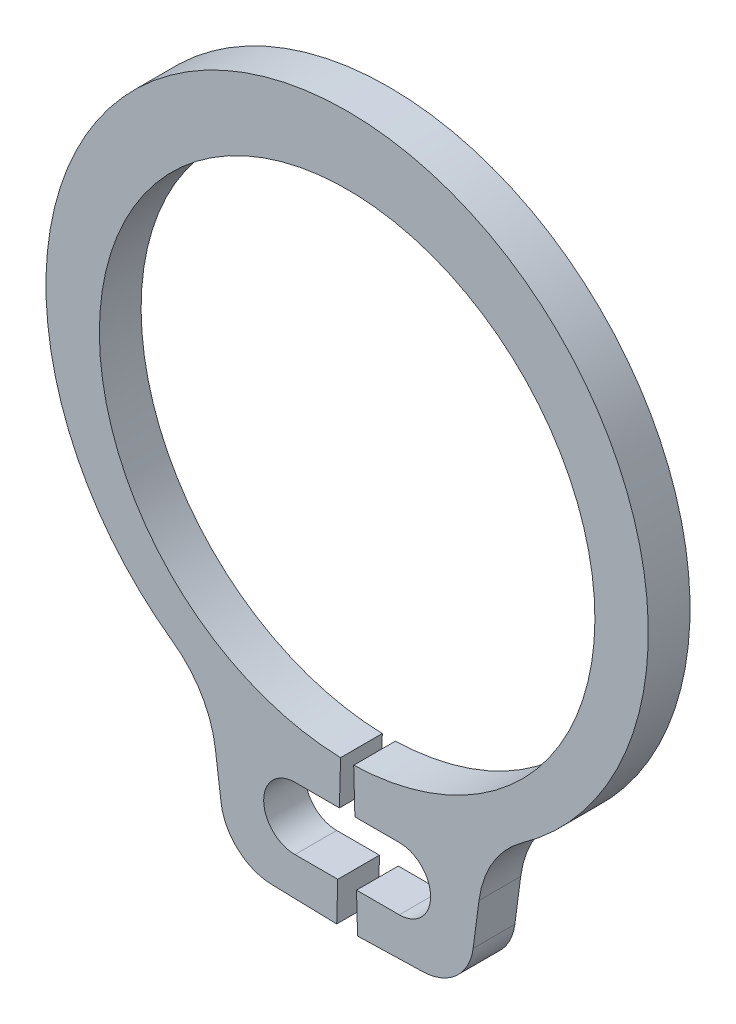
SolidWorks part; units mm, degrees
ref_plane "Plane1" through (0, 0, 0) normal (0, 0, 1) x (1, 0, 0)
ref_plane "Plane2" through (0, 0, 0) normal (0, 1, 0) x (1, 0, 0)
ref_plane "Plane3" through (0, 0, 0) normal (1, 0, 0) x (0, 0, -1)
sketch "Clipboard" plane through (0, 0, 0) normal (0, 0, 1) x (1, 0, 0)
  line L0 (0, 0) -> (0.65, 0)
  line L1 (0, 0) -> (0, 0.4)
  line L2 (0, 0) -> (0, -1.4)
  circle A0 centre (0, 0) radius 0.3
  circle A1 centre (0, 0) radius 2.5
  dimension "HoleDia" = 0.6
  dimension "ShaftDia" = 5
  dimension "LargeSection" = 0.65
  dimension "SmallSection" = 0.4
  dimension "LugSection" = 1.4
sketch "BodySke" plane through (0, 0, 0) normal (0, 0, 1) x (1, 0, 0)
  line L0 (-1.5431, 0) -> (1.5431, 0) construction
  line L1 (0, 0) -> (0, 3.025) construction
  line L2 (0.0629, -2.3742) -> (0.1, -3.7737)
  line L3 (-0.0629, -2.3742) -> (-0.1, -3.7737)
  line L4 (0, 0) -> (2.255, -3.0275) construction
  line L5 (0, 0) -> (-2.255, -3.0275) construction
  line L6 (0.1, -3.7737) -> (0.7253, -3.7571)
  line L7 (1.2638, -2.897) -> (1.2078, -3.3225)
  line L8 (-1.2638, -2.897) -> (-1.2078, -3.3225)
  line L9 (-0.1, -3.7737) -> (-0.7253, -3.7571)
  circle A0 centre (0, 0) radius 2.375 construction
  arc A1 (0.0629, -2.3742) -> (-0.0629, -2.3742) centre (0, 0) ccw
  arc A2 (1.6576, -2.2255) -> (-1.6576, -2.2255) centre (0, 0.1381) ccw construction
  arc A3 (0.1, -3.7737) -> (0.9453, -3.6547) centre (0, 0) ccw construction
  arc A4 (1.6749, -2.2133) -> (1.2638, -2.897) centre (2.255, -3.0275) ccw
  arc A5 (-1.2638, -2.897) -> (-1.6749, -2.2133) centre (-2.255, -3.0275) ccw
  arc A6 (-0.9453, -3.6547) -> (-0.1, -3.7737) centre (0, 0) ccw construction
  arc A7 (1.6749, -2.2133) -> (-1.6749, -2.2133) centre (0, 0.1381) ccw
  arc A8 (-1.2674, -2.8701) -> (1.2674, -2.8701) centre (0, 0) ccw construction
  circle A9 centre (0.5, -3.0974) radius 0.3
  circle A10 centre (-0.5, -3.0974) radius 0.3
  arc A11 (1.2078, -3.3225) -> (0.7253, -3.7571) centre (0.7121, -3.2573) cw
  arc A12 (-1.2078, -3.3225) -> (-0.7253, -3.7571) centre (-0.7121, -3.2573) ccw
  point P28 (1.1728, -3.5882)
  point P31 (-1.1728, -3.5882)
  dimension "GrooveDia" = 4.75
  dimension "D3" = 0.5
  dimension "LugRad" = 3.775
  dimension "HoleOffsetRad" = 3.1375
  dimension "HoleDia" = 0.6
  dimension "D2" = 15
  dimension "LargeRad" = 3.025
  dimension "SmallRad" = 2.775
  dimension "Gap" = 0.2
  dimension "SmallAngle" = 73.359
  dimension "HoleSpacing" = 1
extrude "Body" add sketch "BodySke" against normal blind 0.4
sketch "NotSke" plane through (0, 0, 0) normal (0, 0, 1) x (1, 0, 0)
  line L0 (0.5, -2.7974) -> (0.5, -3.3974)
  line L1 (0.5, -3.3974) -> (-0.5, -3.3974)
  line L2 (-0.5, -3.3974) -> (-0.5, -2.7974)
  line L3 (-0.5, -2.7974) -> (0.5, -2.7974)
  circle A0 centre (0.5, -3.0974) radius 0.3 construction
  circle A1 centre (-0.5, -3.0974) radius 0.3 construction
extrude "Notch" cut sketch "NotSke" against normal through all
equation "' \"ShaftDia@Clipboard\" = 4"
equation "' \"Thickness@Body\" = 0.25"
equation "' \"GrooveDia@BodySke\" = 3.8"
equation "' \"LugSection@Clipboard\" = 1.35"
equation "' \"LargeSection@Clipboard\" = 0.65"
equation "' \"SmallSection@Clipboard\" = 0.4"
equation "' \"HoleDia@Clipboard\" = 0.6"
equation "' \"ShaftDia@Clipboard\" = 15"
equation "' \"Thickness@Body\" = 0.9"
equation "' \"GrooveDia@BodySke\" = 14.15"
equation "' \"LugSection@Clipboard\" = 2.8"
equation "' \"LargeSection@Clipboard\" = 1.8"
equation "' \"SmallSection@Clipboard\" = 1.05"
equation "' \"HoleDia@Clipboard\" = 1.2"
equation "\"Gap@BodySke\" =  \"Thickness@Body\" / 2"
equation "\"LargeRad@BodySke\" =  \"GrooveDia@BodySke\" / 2 +  \"LargeSection@Clipboard\""
equation "\"SmallRad@BodySke\" =  \"GrooveDia@BodySke\" / 2 +  \"SmallSection@Clipboard\""
equation "\"LugRad@BodySke\" = \"GrooveDia@BodySke\" / 2 + \"LugSection@Clipboard\""
equation "\"HoleOffsetRad@BodySke\" = (  \"ShaftDia@Clipboard\" / 2 + \"LugRad@BodySke\" ) / 2"
equation "\"HoleSpacing@BodySke\" = \"Gap@BodySke\"  * 2 +  \"HoleDia@Clipboard\""
equation "\"HoleDia@BodySke\" =  \"HoleDia@Clipboard\""
equation "\"SmallAngle@BodySke\" = atn(\"HoleSpacing@BodySke\" / 2 / sqr(\"HoleOffsetRad@BodySke\"  * \"HoleOffsetRad@BodySke\" - (\"HoleSpacing@BodySke\" / 2) * (\"HoleSpacing@BodySke\" / 2) ))  * 8 * ( 180 / 3.141593)"
